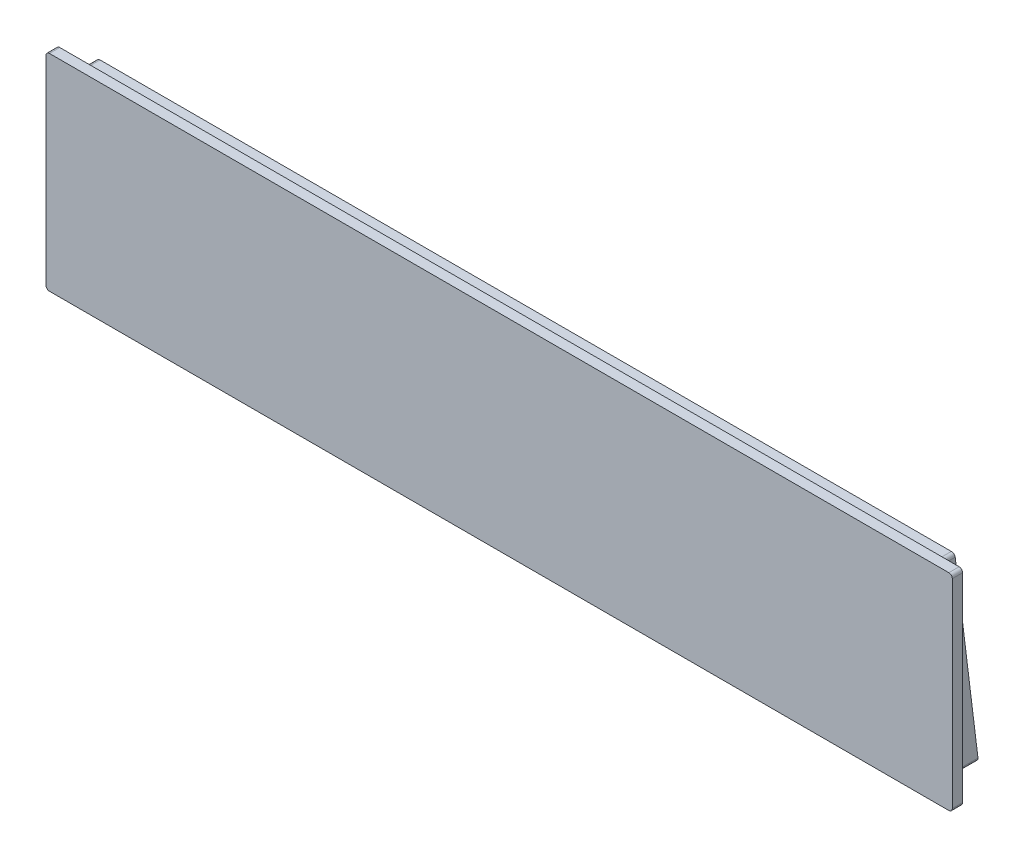
SolidWorks part; units mm, degrees
ref_plane "Front Plane" through (0, 0, 0) normal (0, 0, 1) x (1, 0, 0)
ref_plane "Top Plane" through (0, 0, 0) normal (0, 1, 0) x (1, 0, 0)
ref_plane "Right Plane" through (0, 0, 0) normal (1, 0, 0) x (0, 0, -1)
sketch "Sketch1" plane through (0, 0, 0) normal (0, 0, 1) x (1, 0, 0)
  line L1 (132, -30) -> (-132, -30)
  line L2 (132, -30) -> (132, 30)
  line L3 (132, 30) -> (-132, 30)
  line L4 (-132, -30) -> (-132, 30)
  line L5 (132, -30) -> (-132, 30) construction
  line L6 (132, 30) -> (-132, -30) construction
  point P0 (0, 0)
  dimension "D1" = 264
  dimension "D2" = 60
extrude "Boss-Extrude1" add sketch "Sketch1" along normal blind 3
sketch "Sketch2" plane through (0, 0, 0) normal (1, 0, 0) x (0, 0, -1)
  line L0 (0, 28) -> (4.73, 28)
  line L1 (0, -30) -> (0, 30) construction
  line L2 (4.73, 28) -> (11.6059, -28)
  line L3 (11.6059, -28) -> (0, -28)
  line L4 (0, -28) -> (0, 28)
  line L5 (-3, 30) -> (0, 30) construction
  line L6 (-3, -30) -> (0, -30) construction
  dimension "D1" = 7
  dimension "D2" = 4.73
  dimension "D3" = 2
  dimension "D4" = 2
extrude "Boss-Extrude2" add sketch "Sketch2" along normal offset from surface 7 and the other way offset from surface (125 mm away) 7 up to face at (132, 0, 1.5) other way up to face at (-132, 0, 1.5)
fillet "Fillet1" radius 1 8 edges at (-125, -28, -5.803) (-125, 28, -2.365) (125, 28, -2.365) (125, -28, -5.803) (-132, -30, 1.5) (132, -30, 1.5) (-132, 30, 1.5) (132, 30, 1.5)
